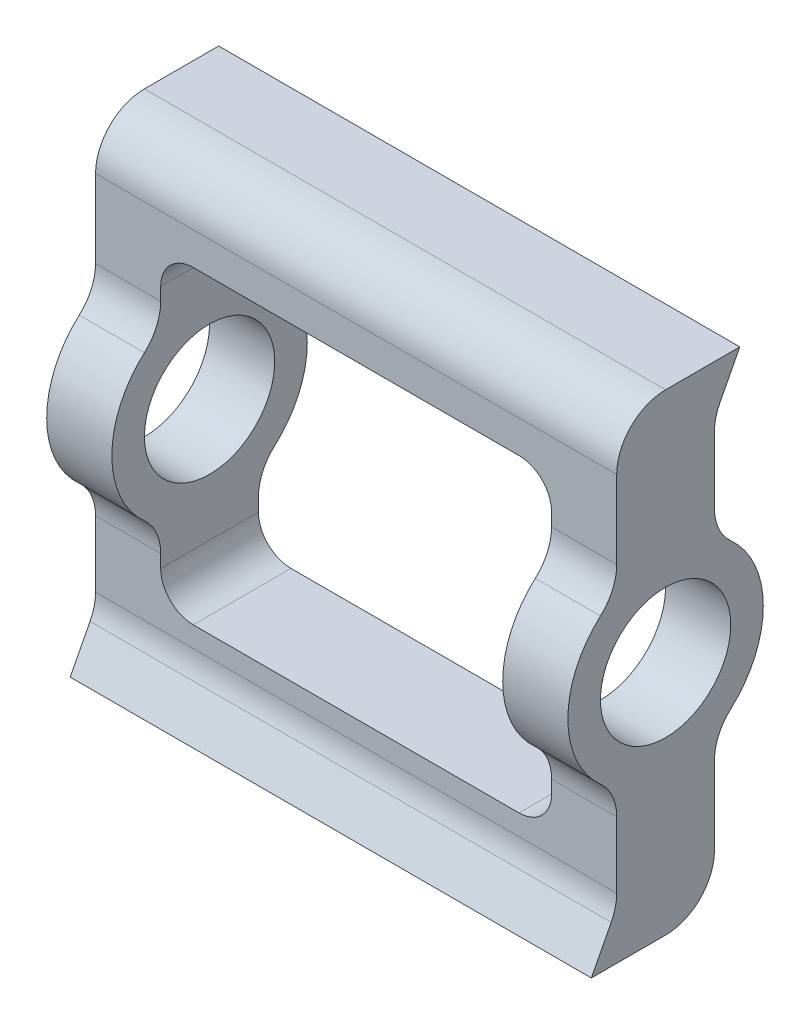
SolidWorks part; units mm, degrees
material "AISI Type A2 Tool Steel"
ref_plane "Front Plane" through (0, 0, 0) normal (0, 0, 1) x (1, 0, 0)
ref_plane "Top Plane" through (0, 0, 0) normal (0, 1, 0) x (1, 0, 0)
ref_plane "Right Plane" through (0, 0, 0) normal (1, 0, 0) x (0, 0, -1)
other "Bounding Box"
ref_plane "Default Plane" through (-8.9266, -12.7485, 0) normal (-0.1736, 0.9848, 0) x (0.9848, 0.1736, 0)
sketch "Sketch1" plane through (0, 0, 0) normal (1, 0, 0) x (0, 0, -1)
  line L0 (9.525, 36.5125) -> (14.4733, 46.0375)
  line L1 (-9.525, -36.5125) -> (9.525, -36.5125) construction
  line L2 (-9.525, -36.5125) -> (-9.525, -16.4978)
  line L3 (-9.525, 36.5125) -> (9.525, 36.5125) construction
  line L4 (9.525, -36.5125) -> (9.525, -16.4978)
  line L5 (-9.525, -36.5125) -> (9.525, 36.5125) construction
  line L6 (-9.525, 36.5125) -> (9.525, -36.5125) construction
  line L7 (14.4733, 46.0375) -> (-9.525, 46.0375)
  line L8 (-9.525, 46.0375) -> (-9.525, 36.5125)
  line L9 (9.525, -36.5125) -> (9.525, -46.0375)
  line L10 (9.525, -46.0375) -> (-14.4733, -46.0375)
  line L11 (-14.4733, -46.0375) -> (-9.525, -36.5125)
  line L12 (-14.4733, -46.0375) -> (0, 0) construction
  line L13 (-9.525, 16.4978) -> (-9.525, 36.5125)
  line L14 (9.525, 16.4978) -> (9.525, 36.5125)
  circle A0 centre (0, 0) radius 12.7
  arc A1 (-9.525, 16.4978) -> (-9.525, -16.4978) centre (0, 0) ccw
  arc A2 (9.525, -16.4978) -> (9.525, 16.4978) centre (0, 0) ccw
  point P0 (0, 0)
  dimension "D5" = 25.4
  dimension "D6" = 38.1
  dimension "D1" = 92.075
  dimension "D2" = 19.05
  dimension "D3" = 10
  dimension "D4" = 9.525
extrude "Boss-Extrude1" add sketch "Sketch1" along normal mid plane 101.6
sketch "Sketch2" plane through (0, 0, 0) normal (0, 0, 1) x (1, 0, 0)
  line L0 (50.8, 46.0375) -> (-50.8, 46.0375) construction
  line L1 (-38.1, -30.1625) -> (38.1, -30.1625)
  line L2 (-38.1, -30.1625) -> (-38.1, 30.1625)
  line L3 (-38.1, 30.1625) -> (38.1, 30.1625)
  line L4 (38.1, -30.1625) -> (38.1, 30.1625)
  line L5 (-38.1, -30.1625) -> (38.1, 30.1625) construction
  line L6 (-38.1, 30.1625) -> (38.1, -30.1625) construction
  line L7 (-50.8, 46.0375) -> (-50.8, 16.4978) construction
  point P0 (0, 0)
  dimension "D1" = 15.875
  dimension "D2" = 12.7
extrude "Cut-Extrude1" cut sketch "Sketch2" against normal through all both and the other way through all
fillet "Fillet1" radius 6.35 4 edges at (-38.1, 30.1625, 0) (38.1, 30.1625, 0) (38.1, -30.1625, 0) (-38.1, -30.1625, 0)
fillet "Fillet2" radius 9.525 8 edges at (-44.45, 16.4978, -9.525) (-44.45, -16.4978, -9.525) (44.45, 16.4978, -9.525) (44.45, -16.4978, -9.525) (-44.45, 16.4978, 9.525) (-44.45, -16.4978, 9.525) (44.45, -16.4978, 9.525) (44.45, 16.4978, 9.525)
fillet "Fillet3" radius 9.525 2 edges at (0, -46.0375, -9.525) (0, 46.0375, 9.525)
fillet "Fillet4" radius 9.525 2 edges at (0, 36.5125, -9.525) (0, -36.5125, 9.525)
